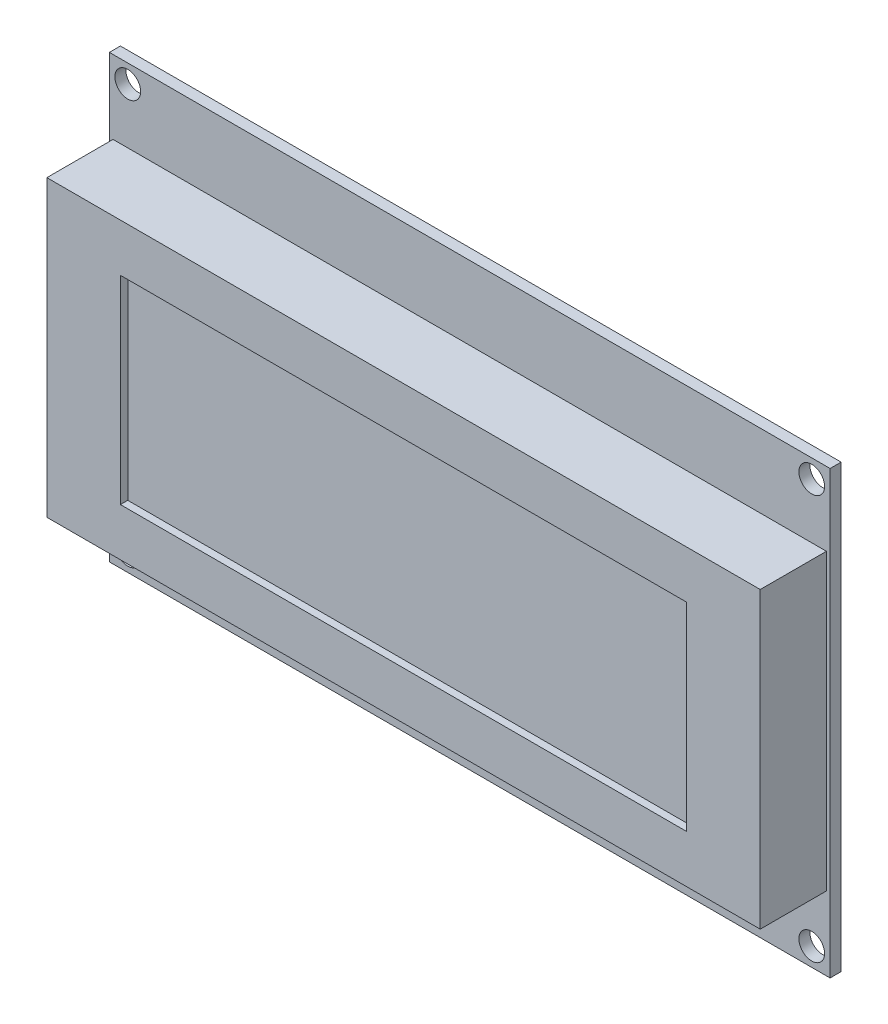
SolidWorks part; units mm, degrees
ref_plane "Front Plane" through (0, 0, 0) normal (0, 0, 1) x (1, 0, 0)
ref_plane "Top Plane" through (0, 0, 0) normal (0, 1, 0) x (1, 0, 0)
ref_plane "Right Plane" through (0, 0, 0) normal (1, 0, 0) x (0, 0, -1)
sketch "Sketch1" plane through (0, 0, 0) normal (0, 0, 1) x (1, 0, 0)
  line L1 (-49, 30) -> (49, 30)
  line L2 (-49, 30) -> (-49, -30)
  line L3 (-49, -30) -> (49, -30)
  line L4 (49, 30) -> (49, -30)
  line L5 (-49, 30) -> (49, -30) construction
  line L6 (-49, -30) -> (49, 30) construction
  point P0 (0, 0)
  dimension "D1" = 98
  dimension "D2" = 60
extrude "Boss-Extrude1" add sketch "Sketch1" along normal blind 1.5
sketch "Sketch2" plane through (0, 0, 1.5) normal (0, 0, 1) x (1, 0, 0)
  line L0 (-49, 30) -> (-49, -30) construction
  line L1 (-49, -20) -> (49, -20)
  line L2 (-49, -20) -> (-49, 20)
  line L3 (-49, 20) -> (49, 20)
  line L4 (49, -20) -> (49, 20)
  line L5 (49, -30) -> (49, 30) construction
  line L6 (-49, -30) -> (49, -30) construction
  dimension "D1" = 10
  dimension "D2" = 40
extrude "Boss-Extrude2" add sketch "Sketch2" along normal blind 9
sketch "Sketch3" plane through (0, 0, 10.5) normal (0, 0, 1) x (1, 0, 0)
  line L0 (0, -20) -> (0, 20) construction
  line L1 (-49, -20) -> (49, -20) construction
  line L2 (49, 20) -> (-49, 20) construction
  line L3 (0, 20) -> (49, 20) construction
  line L4 (49, 20) -> (49, 0) construction
  line L5 (49, -20) -> (49, 20) construction
  line L6 (49, 0) -> (-49, 0) construction
  line L7 (-49, 20) -> (-49, -20) construction
  line L9 (-38.5, 13.5) -> (38.5, 13.5)
  line L10 (-38.5, 13.5) -> (-38.5, -13.5)
  line L11 (-38.5, -13.5) -> (38.5, -13.5)
  line L12 (38.5, 13.5) -> (38.5, -13.5)
  line L13 (-38.5, 13.5) -> (38.5, -13.5) construction
  line L14 (-38.5, -13.5) -> (38.5, 13.5) construction
  point P6 (0, 0)
  dimension "D1" = 27
  dimension "D2" = 77
extrude "Cut-Extrude1" cut sketch "Sketch3" against normal blind 1
sketch "Sketch4" plane through (0, 0, 1.5) normal (0, 0, 1) x (1, 0, 0)
  circle A0 centre (-46.5, 27.5) radius 1.75
  circle A1 centre (46.5, 27.5) radius 1.75
  circle A2 centre (46.5, -27.5) radius 1.75
  circle A3 centre (-46.5, -27.5) radius 1.75
  point P0 (0, 0)
  dimension "D3" = 3.5
  dimension "D4" = 3.5
  dimension "D5" = 3.5
  dimension "D6" = 3.5
  dimension "D1" = 93
  dimension "D2" = 55
extrude "Cut-Extrude2" cut sketch "Sketch4" against normal through all
sketch "Sketch5" plane through (0, 0, 0) normal (0, 0, -1) x (-1, 0, 0)
  line L0 (49, -30) -> (-49, -30) construction
  line L1 (-40, -28) -> (2, -28)
  line L2 (-40, -28) -> (-40, -8)
  line L3 (-40, -8) -> (2, -8)
  line L4 (2, -28) -> (2, -8)
  line L5 (-49, -30) -> (-49, 30) construction
  dimension "D1" = 42
  dimension "D2" = 20
  dimension "D3" = 2
  dimension "D4" = 9
extrude "Boss-Extrude3" add sketch "Sketch5" along normal blind 9
sketch "Sketch6" plane through (0, 0, 10.5) normal (0, 0, 1) x (1, 0, 0)
  line L0 (-49, 20) -> (-49, -20) construction
  line L1 (-48.5, -21.558) -> (-66.9499, -21.558)
  line L2 (-48.5, -21.558) -> (-48.5, 23.1774)
  line L3 (-48.5, 23.1774) -> (-66.9499, 23.1774)
  line L4 (-66.9499, -21.558) -> (-66.9499, 23.1774)
  line L5 (54.2369, -22.8772) -> (48.5, -22.8772)
  line L6 (54.2369, -22.8772) -> (54.2369, 23.1774)
  line L7 (54.2369, 23.1774) -> (48.5, 23.1774)
  line L8 (48.5, -22.8772) -> (48.5, 23.1774)
  line L9 (49, -20) -> (49, 20) construction
  dimension "D1" = 0.5
  dimension "D2" = 0.5
extrude "Cut-Extrude3" cut sketch "Sketch6" against normal up to surface (9 mm away) up to face at (48.25, 27.5, 1.5)
